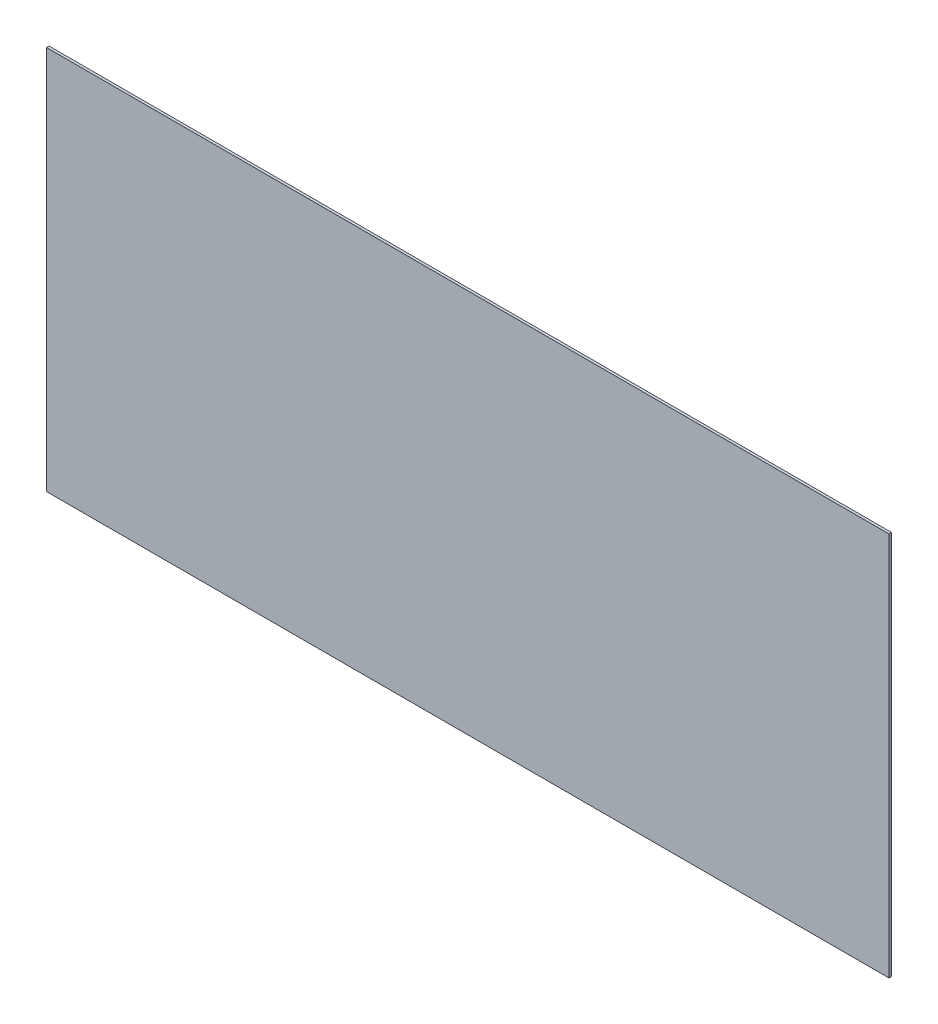
SolidWorks part; units mm, degrees
material "Acrylic (Medium-high impact)"
ref_plane "Front Plane" through (0, 0, 0) normal (0, 0, 1) x (1, 0, 0)
ref_plane "Top Plane" through (0, 0, 0) normal (0, 1, 0) x (1, 0, 0)
ref_plane "Right Plane" through (0, 0, 0) normal (1, 0, 0) x (0, 0, -1)
sketch "Sketch1" plane through (0, 0, 0) normal (0, 0, 1) x (1, 0, 0)
  line L1 (-495.3, 226.06) -> (495.3, 226.06)
  line L2 (-495.3, 226.06) -> (-495.3, -226.06)
  line L3 (-495.3, -226.06) -> (495.3, -226.06)
  line L4 (495.3, 226.06) -> (495.3, -226.06)
  line L5 (-495.3, 226.06) -> (495.3, -226.06) construction
  line L6 (-495.3, -226.06) -> (495.3, 226.06) construction
  point P0 (0, 0)
  dimension "D1" = 990.6
  dimension "D2" = 452.12
extrude "Boss-Extrude1" add sketch "Sketch1" along normal blind 2.9972
